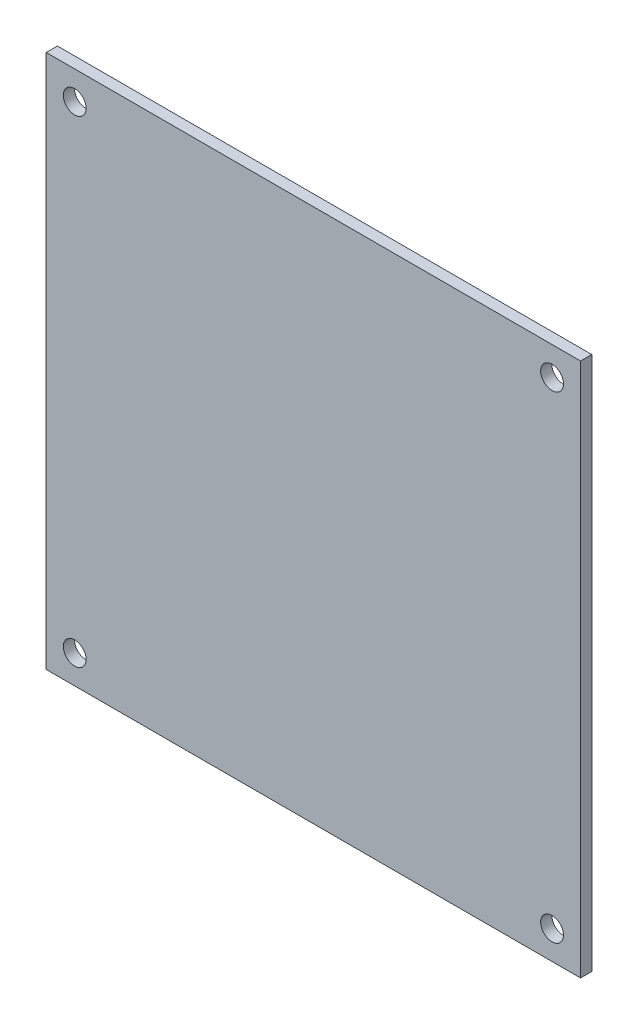
SolidWorks part; units mm, degrees
ref_plane "Front Plane" through (0, 0, 0) normal (0, 0, 1) x (1, 0, 0)
ref_plane "Top Plane" through (0, 0, 0) normal (0, 1, 0) x (1, 0, 0)
ref_plane "Right Plane" through (0, 0, 0) normal (1, 0, 0) x (0, 0, -1)
sketch "Sketch1" plane through (0, 0, 0) normal (0, 0, 1) x (1, 0, 0)
  line L0 (-47.1951, 37.4579) -> (-47.1951, 38.6379)
  line L1 (-50.6951, 38.6379) -> (-50.6951, 37.4579)
  line L2 (-52.8138, -35.5364) -> (-52.8138, -42.4364)
  line L3 (-44.5138, -42.4364) -> (-44.5138, -35.5364)
  line L4 (-6.5538, -35.5364) -> (-6.5538, -42.4364)
  line L5 (1.7462, -42.4364) -> (1.7462, -35.5364)
  line L6 (-37.6138, -35.5364) -> (-37.6138, -42.4364)
  line L7 (-29.3138, -42.4364) -> (-29.3138, -35.5364)
  line L8 (-16.5835, 35.3579) -> (-16.5835, 42.2579)
  line L9 (-24.8835, 42.2579) -> (-24.8835, 35.3579)
  line L10 (-1.3835, 35.3579) -> (-1.3835, 42.2579)
  line L11 (-9.6835, 42.2579) -> (-9.6835, 35.3579)
  line L12 (-21.7538, -35.5364) -> (-21.7538, -42.4364)
  line L13 (-13.4538, -42.4364) -> (-13.4538, -35.5364)
  line L14 (-52.5951, 33.4579) -> (-45.2951, 33.4579)
  line L15 (-45.2951, 37.4579) -> (-52.5951, 37.4579)
  line L16 (-45.2951, 33.4579) -> (-45.2951, 37.4579)
  line L17 (-52.5951, 37.4579) -> (-52.5951, 33.4579)
  line L18 (-50.6951, 38.6379) -> (-47.1951, 38.6379)
  line L19 (-30.2951, 27.4579) -> (-30.2951, 37.4579)
  line L20 (-30.2951, 27.4579) -> (-37.7951, 27.4579)
  line L21 (-37.7951, 27.4579) -> (-37.7951, 37.4579)
  line L22 (-30.2951, 37.4579) -> (-37.7951, 37.4579)
  line L23 (-55.53, -21.1883) -> (-55.53, 14.3717)
  line L24 (-60.61, -21.1883) -> (-55.53, -21.1883)
  line L25 (-60.61, 14.3717) -> (-60.61, -21.1883)
  line L26 (-55.53, 14.3717) -> (-60.61, 14.3717)
  line L27 (3.5091, -18.4116) -> (8.5891, -18.4116)
  line L28 (8.5891, 17.1484) -> (3.5091, 17.1484)
  line L29 (3.5091, 17.1484) -> (3.5091, -18.4116)
  line L30 (8.5891, -18.4116) -> (8.5891, 17.1484)
  line L31 (-43.5638, -28.5364) -> (-53.7638, -28.5364)
  line L32 (-54.2638, -28.0364) -> (-54.2542, -28.046)
  line L33 (-54.2542, -28.046) -> (-54.2258, -28.0745)
  line L34 (-54.2258, -28.0745) -> (-54.1796, -28.1207)
  line L35 (-54.1796, -28.1207) -> (-54.1174, -28.1829)
  line L36 (-54.1174, -28.1829) -> (-54.0416, -28.2587)
  line L37 (-54.0416, -28.2587) -> (-53.9552, -28.3451)
  line L38 (-53.9552, -28.3451) -> (-53.8614, -28.4389)
  line L39 (-53.8614, -28.4389) -> (-53.7638, -28.5364)
  line L40 (-54.2638, -28.0364) -> (-43.0638, -28.0364)
  line L41 (-43.5638, -28.5364) -> (-43.4663, -28.4389)
  line L42 (-43.4663, -28.4389) -> (-43.3725, -28.3451)
  line L43 (-43.3725, -28.3451) -> (-43.2861, -28.2587)
  line L44 (-43.2861, -28.2587) -> (-43.2103, -28.1829)
  line L45 (-43.2103, -28.1829) -> (-43.1481, -28.1207)
  line L46 (-43.1481, -28.1207) -> (-43.1019, -28.0745)
  line L47 (-43.1019, -28.0745) -> (-43.0735, -28.046)
  line L48 (-43.0735, -28.046) -> (-43.0638, -28.0364)
  line L49 (-54.2638, -34.5364) -> (-54.2638, -28.0364)
  line L50 (-53.7638, -28.5364) -> (-53.7638, -34.5364)
  line L51 (-54.2638, -34.5364) -> (-53.7638, -34.5364)
  line L52 (-43.5638, -34.5364) -> (-43.5638, -28.5364)
  line L53 (-43.0638, -28.0364) -> (-43.0638, -34.5364)
  line L54 (-43.5638, -34.5364) -> (-43.0638, -34.5364)
  line L55 (-53.7638, -34.5364) -> (-43.5638, -34.5364)
  line L56 (-43.5638, -34.5364) -> (-43.5638, -35.0364)
  line L57 (-43.5638, -35.0364) -> (-53.7638, -35.0364)
  line L58 (-53.7638, -35.0364) -> (-53.7638, -34.5364)
  line L59 (-45.0138, -42.9364) -> (-52.3138, -42.9364)
  line L60 (-8.0038, -34.5364) -> (-8.0038, -28.0364)
  line L61 (-8.0038, -28.0364) -> (-7.9942, -28.046)
  line L62 (-7.9942, -28.046) -> (-7.9658, -28.0745)
  line L63 (-7.9658, -28.0745) -> (-7.9196, -28.1207)
  line L64 (-7.9196, -28.1207) -> (-7.8574, -28.1829)
  line L65 (-7.8574, -28.1829) -> (-7.7816, -28.2587)
  line L66 (-7.7816, -28.2587) -> (-7.6952, -28.3451)
  line L67 (-7.6952, -28.3451) -> (-7.6014, -28.4389)
  line L68 (-7.6014, -28.4389) -> (-7.5038, -28.5364)
  line L69 (-7.5038, -28.5364) -> (-7.5038, -34.5364)
  line L70 (-8.0038, -34.5364) -> (-7.5038, -34.5364)
  line L71 (2.6962, -28.5364) -> (-7.5038, -28.5364)
  line L72 (-8.0038, -28.0364) -> (3.1962, -28.0364)
  line L73 (2.6962, -28.5364) -> (2.7937, -28.4389)
  line L74 (2.7937, -28.4389) -> (2.8875, -28.3451)
  line L75 (2.8875, -28.3451) -> (2.9739, -28.2587)
  line L76 (2.9739, -28.2587) -> (3.0497, -28.1829)
  line L77 (3.0497, -28.1829) -> (3.1119, -28.1207)
  line L78 (3.1119, -28.1207) -> (3.1581, -28.0745)
  line L79 (3.1581, -28.0745) -> (3.1865, -28.046)
  line L80 (3.1865, -28.046) -> (3.1962, -28.0364)
  line L81 (2.6962, -34.5364) -> (2.6962, -28.5364)
  line L82 (3.1962, -28.0364) -> (3.1962, -34.5364)
  line L83 (2.6962, -34.5364) -> (3.1962, -34.5364)
  line L84 (-7.5038, -34.5364) -> (2.6962, -34.5364)
  line L85 (2.6962, -34.5364) -> (2.6962, -35.0364)
  line L86 (2.6962, -35.0364) -> (-7.5038, -35.0364)
  line L87 (-7.5038, -35.0364) -> (-7.5038, -34.5364)
  line L88 (1.2462, -42.9364) -> (-6.0538, -42.9364)
  line L89 (-28.3638, -34.5364) -> (-28.3638, -28.5364)
  line L90 (-28.3638, -28.5364) -> (-28.2663, -28.4389)
  line L91 (-28.2663, -28.4389) -> (-28.1725, -28.3451)
  line L92 (-28.1725, -28.3451) -> (-28.0861, -28.2587)
  line L93 (-28.0861, -28.2587) -> (-28.0103, -28.1829)
  line L94 (-28.0103, -28.1829) -> (-27.9481, -28.1207)
  line L95 (-27.9481, -28.1207) -> (-27.9019, -28.0745)
  line L96 (-27.9019, -28.0745) -> (-27.8735, -28.046)
  line L97 (-27.8735, -28.046) -> (-27.8638, -28.0364)
  line L98 (-27.8638, -28.0364) -> (-27.8638, -34.5364)
  line L99 (-28.3638, -34.5364) -> (-27.8638, -34.5364)
  line L100 (-39.0638, -34.5364) -> (-39.0638, -28.0364)
  line L101 (-39.0638, -28.0364) -> (-39.0542, -28.046)
  line L102 (-39.0542, -28.046) -> (-39.0258, -28.0745)
  line L103 (-39.0258, -28.0745) -> (-38.9796, -28.1207)
  line L104 (-38.9796, -28.1207) -> (-38.9174, -28.1829)
  line L105 (-38.9174, -28.1829) -> (-38.8416, -28.2587)
  line L106 (-38.8416, -28.2587) -> (-38.7552, -28.3451)
  line L107 (-38.7552, -28.3451) -> (-38.6614, -28.4389)
  line L108 (-38.6614, -28.4389) -> (-38.5638, -28.5364)
  line L109 (-38.5638, -28.5364) -> (-38.5638, -34.5364)
  line L110 (-39.0638, -34.5364) -> (-38.5638, -34.5364)
  line L111 (-28.3638, -28.5364) -> (-38.5638, -28.5364)
  line L112 (-39.0638, -28.0364) -> (-27.8638, -28.0364)
  line L113 (-38.5638, -34.5364) -> (-28.3638, -34.5364)
  line L114 (-28.3638, -34.5364) -> (-28.3638, -35.0364)
  line L115 (-38.5638, -35.0364) -> (-38.5638, -34.5364)
  line L116 (-28.3638, -35.0364) -> (-38.5638, -35.0364)
  line L117 (-29.8138, -42.9364) -> (-37.1138, -42.9364)
  line L118 (-15.6335, 34.3579) -> (-25.8335, 34.3579)
  line L119 (-25.8335, 34.3579) -> (-25.8335, 34.8579)
  line L120 (-25.8335, 34.8579) -> (-15.6335, 34.8579)
  line L121 (-15.6335, 34.8579) -> (-15.6335, 34.3579)
  line L122 (-15.1335, 34.3579) -> (-15.6335, 34.3579)
  line L123 (-25.8335, 34.3579) -> (-26.3335, 34.3579)
  line L124 (-15.6335, 28.3579) -> (-15.6335, 34.3579)
  line L125 (-25.8335, 28.3579) -> (-15.6335, 28.3579)
  line L126 (-25.8335, 34.3579) -> (-25.8335, 28.3579)
  line L127 (-25.8335, 28.3579) -> (-25.931, 28.2604)
  line L128 (-25.931, 28.2604) -> (-26.0248, 28.1666)
  line L129 (-26.0248, 28.1666) -> (-26.1113, 28.0801)
  line L130 (-26.1113, 28.0801) -> (-26.187, 28.0044)
  line L131 (-26.187, 28.0044) -> (-26.2492, 27.9422)
  line L132 (-26.2492, 27.9422) -> (-26.2954, 27.896)
  line L133 (-26.2954, 27.896) -> (-26.3239, 27.8675)
  line L134 (-26.3239, 27.8675) -> (-26.3335, 27.8579)
  line L135 (-26.3335, 27.8579) -> (-26.3335, 34.3579)
  line L136 (-15.1335, 34.3579) -> (-15.1335, 27.8579)
  line L137 (-15.1335, 27.8579) -> (-15.1431, 27.8675)
  line L138 (-15.1431, 27.8675) -> (-15.1715, 27.896)
  line L139 (-15.1715, 27.896) -> (-15.2177, 27.9422)
  line L140 (-15.2177, 27.9422) -> (-15.2799, 28.0044)
  line L141 (-15.2799, 28.0044) -> (-15.3557, 28.0801)
  line L142 (-15.3557, 28.0801) -> (-15.4421, 28.1666)
  line L143 (-15.4421, 28.1666) -> (-15.5359, 28.2604)
  line L144 (-15.5359, 28.2604) -> (-15.6335, 28.3579)
  line L145 (-15.1335, 27.8579) -> (-26.3335, 27.8579)
  line L146 (-24.3835, 42.7579) -> (-17.0835, 42.7579)
  line L147 (-10.6335, 34.3579) -> (-11.1335, 34.3579)
  line L148 (-10.6335, 34.3579) -> (-10.6335, 34.8579)
  line L149 (-0.4335, 34.3579) -> (-10.6335, 34.3579)
  line L150 (-10.6335, 34.8579) -> (-0.4335, 34.8579)
  line L151 (-0.4335, 34.8579) -> (-0.4335, 34.3579)
  line L152 (0.0665, 34.3579) -> (-0.4335, 34.3579)
  line L153 (0.0665, 34.3579) -> (0.0665, 27.8579)
  line L154 (0.0665, 27.8579) -> (-0.4335, 28.3579)
  line L155 (-0.4335, 28.3579) -> (-0.4335, 34.3579)
  line L156 (-10.6335, 34.3579) -> (-10.6335, 28.3579)
  line L157 (-10.6335, 28.3579) -> (-10.731, 28.2604)
  line L158 (-10.731, 28.2604) -> (-10.8248, 28.1666)
  line L159 (-10.8248, 28.1666) -> (-10.9113, 28.0801)
  line L160 (-10.9113, 28.0801) -> (-10.987, 28.0044)
  line L161 (-10.987, 28.0044) -> (-11.0492, 27.9422)
  line L162 (-11.0492, 27.9422) -> (-11.0954, 27.896)
  line L163 (-11.0954, 27.896) -> (-11.1239, 27.8675)
  line L164 (-11.1239, 27.8675) -> (-11.1335, 27.8579)
  line L165 (-11.1335, 27.8579) -> (-11.1335, 34.3579)
  line L166 (-10.6335, 28.3579) -> (-0.4335, 28.3579)
  line L167 (0.0665, 27.8579) -> (-11.1335, 27.8579)
  line L168 (-9.1835, 42.7579) -> (-1.8835, 42.7579)
  line L169 (-12.5038, -34.5364) -> (-12.5038, -28.5364)
  line L170 (-12.5038, -28.5364) -> (-12.4063, -28.4389)
  line L171 (-12.4063, -28.4389) -> (-12.3125, -28.3451)
  line L172 (-12.3125, -28.3451) -> (-12.2261, -28.2587)
  line L173 (-12.2261, -28.2587) -> (-12.1503, -28.1829)
  line L174 (-12.1503, -28.1829) -> (-12.0881, -28.1207)
  line L175 (-12.0881, -28.1207) -> (-12.0419, -28.0745)
  line L176 (-12.0419, -28.0745) -> (-12.0135, -28.046)
  line L177 (-12.0135, -28.046) -> (-12.0038, -28.0364)
  line L178 (-12.0038, -28.0364) -> (-12.0038, -34.5364)
  line L179 (-12.5038, -34.5364) -> (-12.0038, -34.5364)
  line L180 (-12.5038, -28.5364) -> (-22.7038, -28.5364)
  line L181 (-23.2038, -28.0364) -> (-23.1942, -28.046)
  line L182 (-23.1942, -28.046) -> (-23.1658, -28.0745)
  line L183 (-23.1658, -28.0745) -> (-23.1196, -28.1207)
  line L184 (-23.1196, -28.1207) -> (-23.0574, -28.1829)
  line L185 (-23.0574, -28.1829) -> (-22.9816, -28.2587)
  line L186 (-22.9816, -28.2587) -> (-22.8952, -28.3451)
  line L187 (-22.8952, -28.3451) -> (-22.8014, -28.4389)
  line L188 (-22.8014, -28.4389) -> (-22.7038, -28.5364)
  line L189 (-23.2038, -28.0364) -> (-12.0038, -28.0364)
  line L190 (-23.2038, -34.5364) -> (-23.2038, -28.0364)
  line L191 (-22.7038, -28.5364) -> (-22.7038, -34.5364)
  line L192 (-23.2038, -34.5364) -> (-22.7038, -34.5364)
  line L193 (-22.7038, -34.5364) -> (-12.5038, -34.5364)
  line L194 (-22.7038, -35.0364) -> (-22.7038, -34.5364)
  line L195 (-12.5038, -34.5364) -> (-12.5038, -35.0364)
  line L196 (-12.5038, -35.0364) -> (-22.7038, -35.0364)
  line L197 (-13.9538, -42.9364) -> (-21.2538, -42.9364)
  line L198 (11.7049, 37.4579) -> (-1.3835, 37.4579)
  line L199 (-9.6835, 37.4579) -> (-16.5835, 37.4579)
  line L200 (-24.8835, 37.4579) -> (-30.2951, 37.4579)
  line L201 (-37.7951, 37.4579) -> (-45.2951, 37.4579)
  line L202 (-52.5951, 37.4579) -> (-63.2951, 37.4579)
  line L203 (11.7049, -37.5421) -> (11.7049, 37.4579)
  line L204 (-63.2951, -37.5421) -> (-52.8138, -37.5421)
  line L205 (-44.5138, -37.5421) -> (-37.6138, -37.5421)
  line L206 (-29.3138, -37.5421) -> (-21.7538, -37.5421)
  line L207 (-13.4538, -37.5421) -> (-6.5538, -37.5421)
  line L208 (1.7462, -37.5421) -> (11.7049, -37.5421)
  line L209 (-63.2951, 37.4579) -> (-63.2951, -37.5421)
  line L210 (-44.5138, -35.5364) -> (-52.8138, -35.5364)
  line L211 (-52.8138, -42.4364) -> (-44.5138, -42.4364)
  line L212 (1.7462, -35.5364) -> (-6.5538, -35.5364)
  line L213 (-6.5538, -42.4364) -> (1.7462, -42.4364)
  line L214 (-29.3138, -35.5364) -> (-37.6138, -35.5364)
  line L215 (-37.6138, -42.4364) -> (-29.3138, -42.4364)
  line L216 (-24.8835, 35.3579) -> (-16.5835, 35.3579)
  line L217 (-16.5835, 42.2579) -> (-24.8835, 42.2579)
  line L218 (-9.6835, 35.3579) -> (-1.3835, 35.3579)
  line L219 (-1.3835, 42.2579) -> (-9.6835, 42.2579)
  line L220 (-13.4538, -35.5364) -> (-21.7538, -35.5364)
  line L221 (-21.7538, -42.4364) -> (-13.4538, -42.4364)
  arc A0 (-52.8138, -35.5364) -> (-53.3138, -35.0364) centre (-53.3138, -35.5364) ccw
  arc A1 (-44.0138, -35.0364) -> (-44.5138, -35.5364) centre (-44.0138, -35.5364) ccw
  arc A2 (-45.0138, -42.9364) -> (-44.5138, -42.4364) centre (-45.0138, -42.4364) ccw
  arc A3 (-52.8138, -42.4364) -> (-52.3138, -42.9364) centre (-52.3138, -42.4364) ccw
  arc A4 (-6.5538, -35.5364) -> (-7.0538, -35.0364) centre (-7.0538, -35.5364) ccw
  arc A5 (2.2462, -35.0364) -> (1.7462, -35.5364) centre (2.2462, -35.5364) ccw
  arc A6 (1.2462, -42.9364) -> (1.7462, -42.4364) centre (1.2462, -42.4364) ccw
  arc A7 (-6.5538, -42.4364) -> (-6.0538, -42.9364) centre (-6.0538, -42.4364) ccw
  arc A8 (-37.6138, -35.5364) -> (-38.1138, -35.0364) centre (-38.1138, -35.5364) ccw
  arc A9 (-28.8138, -35.0364) -> (-29.3138, -35.5364) centre (-28.8138, -35.5364) ccw
  arc A10 (-29.8138, -42.9364) -> (-29.3138, -42.4364) centre (-29.8138, -42.4364) ccw
  arc A11 (-37.6138, -42.4364) -> (-37.1138, -42.9364) centre (-37.1138, -42.4364) ccw
  arc A12 (-16.5835, 35.3579) -> (-16.0835, 34.8579) centre (-16.0835, 35.3579) ccw
  arc A13 (-25.3835, 34.8579) -> (-24.8835, 35.3579) centre (-25.3835, 35.3579) ccw
  arc A14 (-24.3835, 42.7579) -> (-24.8835, 42.2579) centre (-24.3835, 42.2579) ccw
  arc A15 (-16.5835, 42.2579) -> (-17.0835, 42.7579) centre (-17.0835, 42.2579) ccw
  arc A16 (-1.3835, 35.3579) -> (-0.8835, 34.8579) centre (-0.8835, 35.3579) ccw
  arc A17 (-10.1835, 34.8579) -> (-9.6835, 35.3579) centre (-10.1835, 35.3579) ccw
  arc A18 (-9.1835, 42.7579) -> (-9.6835, 42.2579) centre (-9.1835, 42.2579) ccw
  arc A19 (-1.3835, 42.2579) -> (-1.8835, 42.7579) centre (-1.8835, 42.2579) ccw
  arc A20 (-21.7538, -35.5364) -> (-22.2538, -35.0364) centre (-22.2538, -35.5364) ccw
  arc A21 (-12.9538, -35.0364) -> (-13.4538, -35.5364) centre (-12.9538, -35.5364) ccw
  arc A22 (-13.9538, -42.9364) -> (-13.4538, -42.4364) centre (-13.9538, -42.4364) ccw
  arc A23 (-21.7538, -42.4364) -> (-21.2538, -42.9364) centre (-21.2538, -42.4364) ccw
  arc A24 (-43.5638, -35.0364) -> (-43.0638, -34.5364) centre (-43.5638, -34.5364) ccw
  arc A25 (-54.2638, -34.5364) -> (-53.7638, -35.0364) centre (-53.7638, -34.5364) ccw
  arc A26 (2.6962, -35.0364) -> (3.1962, -34.5364) centre (2.6962, -34.5364) ccw
  arc A27 (-8.0038, -34.5364) -> (-7.5038, -35.0364) centre (-7.5038, -34.5364) ccw
  arc A28 (-28.3638, -35.0364) -> (-27.8638, -34.5364) centre (-28.3638, -34.5364) ccw
  arc A29 (-39.0638, -34.5364) -> (-38.5638, -35.0364) centre (-38.5638, -34.5364) ccw
  arc A30 (-15.1335, 34.3579) -> (-15.6335, 34.8579) centre (-15.6335, 34.3579) ccw
  arc A31 (-25.8335, 34.8579) -> (-26.3335, 34.3579) centre (-25.8335, 34.3579) ccw
  arc A32 (-10.6335, 34.8579) -> (-11.1335, 34.3579) centre (-10.6335, 34.3579) ccw
  arc A33 (0.0665, 34.3579) -> (-0.4335, 34.8579) centre (-0.4335, 34.3579) ccw
  arc A34 (-23.2038, -34.5364) -> (-22.7038, -35.0364) centre (-22.7038, -34.5364) ccw
  arc A35 (-12.5038, -35.0364) -> (-12.0038, -34.5364) centre (-12.5038, -34.5364) ccw
  circle A36 centre (-59.2951, 33.4579) radius 1.6
  circle A37 centre (7.7049, 33.4579) radius 1.6
  circle A38 centre (-59.2951, -33.5421) radius 1.6
  circle A39 centre (7.7049, -33.5421) radius 1.6
sketch "Sketch2" plane through (0, 0, 0) normal (0, 0, 1) x (1, 0, 0)
  line L1 (-63.2951, 37.4579) -> (11.7049, 37.4579)
  line L2 (-63.2951, 37.4579) -> (-63.2951, -37.5421)
  line L3 (-63.2951, -37.5421) -> (11.7049, -37.5421)
  line L4 (11.7049, 37.4579) -> (11.7049, -37.5421)
  circle A0 centre (-59.2951, 33.4579) radius 1.6
  circle A1 centre (7.7049, 33.4579) radius 1.6
  circle A2 centre (-59.2951, -33.5421) radius 1.6
  circle A3 centre (7.7049, -33.5421) radius 1.6
extrude "Boss-Extrude1" add sketch "Sketch2" along normal blind 1.5748
